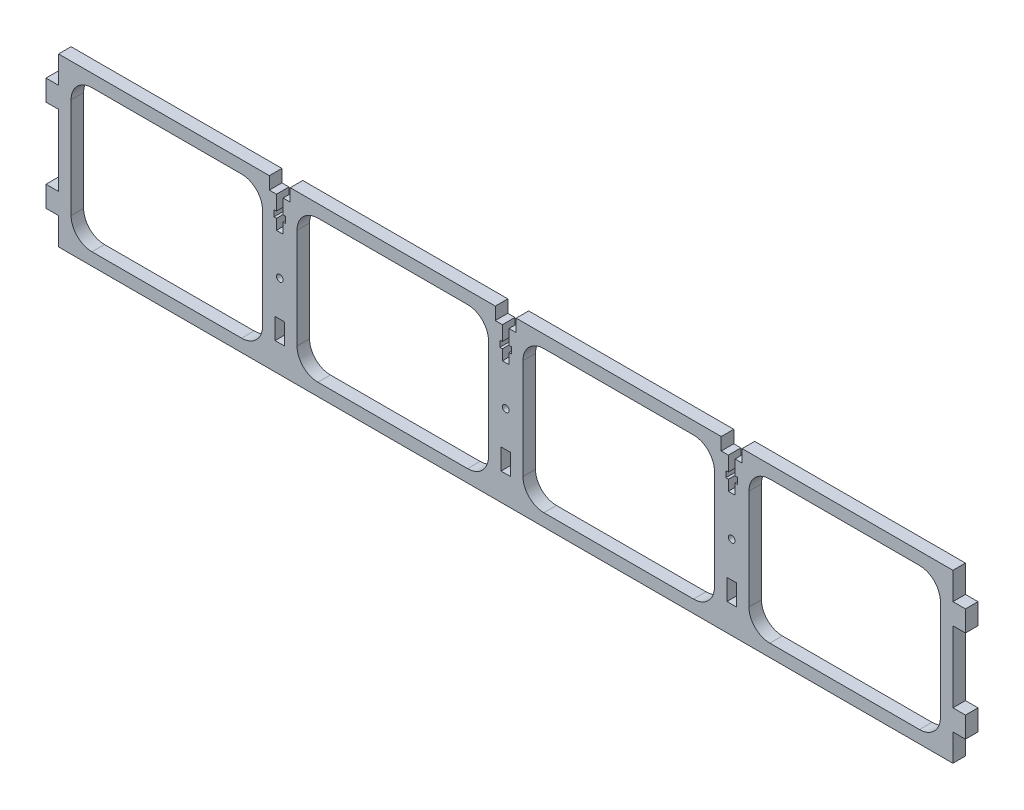
SolidWorks part; units mm, degrees
ref_plane "Front Plane" through (0, 0, 0) normal (0, 0, 1) x (1, 0, 0)
ref_plane "Top Plane" through (0, 0, 0) normal (0, 1, 0) x (1, 0, 0)
ref_plane "Right Plane" through (0, 0, 0) normal (1, 0, 0) x (0, 0, -1)
sketch "Sketch1" plane through (0, 0, 0) normal (0, 0, 1) x (1, 0, 0)
  line L1 (-214, -40) -> (214, -40)
  line L2 (-214, -40) -> (-214, 40)
  line L3 (-214, 40) -> (214, 40)
  line L4 (214, -40) -> (214, 40)
  line L5 (-214, -40) -> (214, 40) construction
  line L6 (-214, 40) -> (214, -40) construction
  point P0 (0, 0)
  dimension "D1" = 428
  dimension "D2" = 80
extrude "Boss-Extrude1" add sketch "Sketch1" along normal blind 6
sketch "Sketch2" plane through (0, 0, 6) normal (0, 0, 1) x (1, 0, 0)
  line L0 (-116.375, -40) -> (-116.375, -27) construction
  line L1 (-208, 40) -> (-208, -40) construction
  line L2 (-214, -34) -> (214, -34) construction
  line L3 (-214, -40) -> (214, -40) construction
  line L8 (214, -40) -> (214, 40)
  line L9 (214, 40) -> (-214, 40)
  line L10 (-214, 40) -> (-214, -40)
  line L11 (-214, -40) -> (214, -40)
  line L12 (214, -40) -> (214, 40) construction
  line L13 (214, 40) -> (-214, 40)
  line L14 (-214, 40) -> (-214, -40) construction
  line L15 (-208, -40) -> (214, -40) construction
  line L16 (-110.375, -40) -> (-110.375, -27) construction
  line L17 (-110.375, -40) -> (-110.375, -27) construction
  line L18 (-116.375, -24) -> (-116.375, 24)
  line L19 (-198, -34) -> (-126.375, -34)
  line L20 (-208, 24) -> (-208, -24)
  line L21 (-126.375, 34) -> (-198, 34)
  arc A0 (-198, 34) -> (-208, 24) centre (-198, 24) ccw
  arc A1 (-126.375, 34) -> (-116.375, 24) centre (-126.375, 24) cw
  arc A2 (-116.375, -24) -> (-126.375, -34) centre (-126.375, -24) cw
  arc A3 (-198, -34) -> (-208, -24) centre (-198, -24) cw
  dimension "D6" = 10
  dimension "D5" = 6
  dimension "D1" = 0
  dimension "D2" = 6
  dimension "D3" = 6
  dimension "D4" = 6
extrude "Cut-Extrude1" cut sketch "Sketch2" against normal up to next (6 mm away) contours L18 L21 L20 L19
pattern_linear "LPattern1" count 4 spacing 108.125 along (1, 0, 0) of "Cut-Extrude1"
sketch "Sketch3" plane through (0, 0, 0) normal (0, 0, -1) x (-1, 0, 0)
  line L8 (-110.375, -27) -> (-110.375, -17) construction
  line L9 (-110.375, -17) -> (-105.875, -17) construction
  line L11 (-105.875, -27) -> (-110.375, -27) construction
  line L24 (-110.375, -27) -> (-110.375, -17)
  line L25 (-110.375, -17) -> (-105.875, -17)
  line L26 (-105.875, -17) -> (-105.875, -27)
  line L27 (-105.875, -27) -> (-110.375, -27)
  line L44 (-2.25, -27) -> (-2.25, -17) construction
  line L45 (-2.25, -17) -> (2.25, -17) construction
  line L46 (2.25, -17) -> (2.25, -27) construction
  line L47 (2.25, -27) -> (-2.25, -27) construction
  line L52 (-2.25, -27) -> (-2.25, -17)
  line L53 (-2.25, -17) -> (2.25, -17)
  line L54 (2.25, -17) -> (2.25, -27)
  line L55 (2.25, -27) -> (-2.25, -27)
  line L60 (105.875, -27) -> (105.875, -17) construction
  line L61 (105.875, -17) -> (110.375, -17) construction
  line L62 (110.375, -17) -> (110.375, -27) construction
  line L63 (110.375, -27) -> (105.875, -27) construction
  line L68 (105.875, -27) -> (105.875, -17)
  line L69 (105.875, -17) -> (110.375, -17)
  line L70 (110.375, -17) -> (110.375, -27)
  line L71 (110.375, -27) -> (105.875, -27)
  circle A3 centre (108.125, 0) radius 1.6 construction
  circle A4 centre (0, 0) radius 1.6 construction
  circle A5 centre (-108.125, 0) radius 1.6 construction
  circle A6 centre (108.125, 0) radius 1.6
  circle A7 centre (0, 0) radius 1.6
  circle A8 centre (-108.125, 0) radius 1.6
extrude "Cut-Extrude2" cut sketch "Sketch3" against normal through all
sketch "Sketch4" plane through (0, 0, 0) normal (0, 0, -1) x (-1, 0, 0)
  line L0 (-111.5, 17) -> (-214, 17) construction
  line L1 (-214, -40) -> (-214, 40) construction
  line L2 (-108.5, 0) -> (-214, 0) construction
  line L3 (-220, 21.3321) -> (-220, 40) construction
  line L4 (-214, 17) -> (-220, 17)
  line L5 (-214, 17) -> (-214, 27)
  line L6 (-214, 27) -> (-220, 27)
  line L7 (-220, 17) -> (-220, 27)
  line L9 (-220, -17) -> (-220, -27)
  line L10 (-214, -27) -> (-220, -27)
  line L11 (-214, -17) -> (-214, -27)
  line L12 (-214, -17) -> (-220, -17)
  line L13 (0, 0) -> (0, 40) construction
  line L14 (-214, 40) -> (214, 40) construction
  line L15 (214, -17) -> (220, -17)
  line L16 (214, -17) -> (214, -27)
  line L17 (214, -27) -> (220, -27)
  line L18 (220, -17) -> (220, -27)
  line L19 (220, 17) -> (220, 27)
  line L20 (214, 27) -> (220, 27)
  line L21 (214, 17) -> (214, 27)
  line L22 (214, 17) -> (220, 17)
  point P13 (-108.5, -1)
  dimension "D1" = 34
  dimension "D2" = 10
extrude "Boss-Extrude2" add sketch "Sketch4" against normal blind 6
sketch "Sketch5" plane through (0, 40, 0) normal (0, 1, 0) x (1, 0, 0)
  line L0 (214, -6) -> (-214, -6) construction
  line L1 (-113.125, 0) -> (-103.125, 0)
  line L2 (-113.125, 0) -> (-113.125, -6)
  line L3 (-113.125, -6) -> (-103.125, -6)
  line L4 (-103.125, 0) -> (-103.125, -6)
  line L5 (-113.125, 0) -> (-103.125, -6) construction
  line L6 (-113.125, -6) -> (-103.125, 0) construction
  line L7 (-103.125, -6) -> (-103.125, 0) construction
  line L8 (5, -6) -> (5, 0) construction
  line L9 (-5, 0) -> (5, 0)
  line L10 (-5, 0) -> (-5, -6)
  line L11 (-5, -6) -> (5, -6)
  line L12 (5, 0) -> (5, -6)
  line L13 (-5, 0) -> (5, -6) construction
  line L14 (-5, -6) -> (5, 0) construction
  line L15 (113.125, -6) -> (113.125, 0) construction
  line L16 (103.125, 0) -> (113.125, 0)
  line L17 (103.125, 0) -> (103.125, -6)
  line L18 (103.125, -6) -> (113.125, -6)
  line L19 (113.125, 0) -> (113.125, -6)
  line L20 (103.125, 0) -> (113.125, -6) construction
  line L21 (103.125, -6) -> (113.125, 0) construction
  point P0 (-108.125, -3)
  point P10 (0, -3)
  point P18 (108.125, -3)
extrude "Cut-Extrude3" cut sketch "Sketch5" against normal blind 6
sketch "Sketch6" plane through (0, 0, 0) normal (0, 0, -1) x (-1, 0, 0)
  line L12 (-109.725, 34) -> (-109.725, 27)
  line L13 (-106.525, 34) -> (-109.725, 34)
  line L14 (-106.525, 27) -> (-106.525, 34)
  line L15 (-105.325, 27) -> (-106.525, 27)
  line L16 (-105.325, 24) -> (-105.325, 27)
  line L17 (-106.525, 24) -> (-105.325, 24)
  line L18 (-106.525, 19) -> (-106.525, 24)
  line L19 (-109.725, 19) -> (-106.525, 19)
  line L20 (-109.725, 24) -> (-109.725, 19)
  line L21 (-110.925, 24) -> (-109.725, 24)
  line L22 (-110.925, 27) -> (-110.925, 24)
  line L23 (-109.725, 27) -> (-110.925, 27)
  line L24 (-109.725, 34) -> (-109.725, 27)
  line L25 (-106.525, 34) -> (-109.725, 34)
  line L26 (-106.525, 27) -> (-106.525, 34)
  line L27 (-105.325, 27) -> (-106.525, 27)
  line L28 (-105.325, 24) -> (-105.325, 27)
  line L29 (-106.525, 24) -> (-105.325, 24)
  line L30 (-106.525, 19) -> (-106.525, 24)
  line L31 (-109.725, 19) -> (-106.525, 19)
  line L32 (-109.725, 24) -> (-109.725, 19)
  line L33 (-110.925, 24) -> (-109.725, 24)
  line L34 (-110.925, 27) -> (-110.925, 24)
  line L35 (-109.725, 27) -> (-110.925, 27)
  line L36 (-1.595, 27) -> (-2.795, 27)
  line L37 (-2.795, 27) -> (-2.795, 24)
  line L38 (-2.795, 24) -> (-1.595, 24)
  line L39 (-1.595, 24) -> (-1.595, 19)
  line L40 (-1.595, 19) -> (1.605, 19)
  line L41 (1.605, 19) -> (1.605, 24)
  line L42 (1.605, 24) -> (2.805, 24)
  line L43 (2.805, 24) -> (2.805, 27)
  line L44 (2.805, 27) -> (1.605, 27)
  line L45 (1.605, 27) -> (1.605, 34)
  line L46 (1.605, 34) -> (-1.595, 34)
  line L47 (-1.595, 34) -> (-1.595, 27)
  line L48 (-1.595, 27) -> (-2.795, 27)
  line L49 (-2.795, 27) -> (-2.795, 24)
  line L50 (-2.795, 24) -> (-1.595, 24)
  line L51 (-1.595, 24) -> (-1.595, 19)
  line L52 (-1.595, 19) -> (1.605, 19)
  line L53 (1.605, 19) -> (1.605, 24)
  line L54 (1.605, 24) -> (2.805, 24)
  line L55 (2.805, 24) -> (2.805, 27)
  line L56 (2.805, 27) -> (1.605, 27)
  line L57 (1.605, 27) -> (1.605, 34)
  line L58 (1.605, 34) -> (-1.595, 34)
  line L59 (-1.595, 34) -> (-1.595, 27)
  line L60 (106.535, 34) -> (106.535, 27)
  line L61 (109.735, 34) -> (106.535, 34)
  line L62 (109.735, 27) -> (109.735, 34)
  line L63 (110.935, 27) -> (109.735, 27)
  line L64 (110.935, 24) -> (110.935, 27)
  line L65 (109.735, 24) -> (110.935, 24)
  line L66 (109.735, 19) -> (109.735, 24)
  line L67 (106.535, 19) -> (109.735, 19)
  line L68 (106.535, 24) -> (106.535, 19)
  line L69 (105.335, 24) -> (106.535, 24)
  line L70 (105.335, 27) -> (105.335, 24)
  line L71 (106.535, 27) -> (105.335, 27)
  line L72 (106.535, 34) -> (106.535, 27)
  line L73 (109.735, 34) -> (106.535, 34)
  line L74 (109.735, 27) -> (109.735, 34)
  line L75 (110.935, 27) -> (109.735, 27)
  line L76 (110.935, 24) -> (110.935, 27)
  line L77 (109.735, 24) -> (110.935, 24)
  line L78 (109.735, 19) -> (109.735, 24)
  line L79 (106.535, 19) -> (109.735, 19)
  line L80 (106.535, 24) -> (106.535, 19)
  line L81 (105.335, 24) -> (106.535, 24)
  line L82 (105.335, 27) -> (105.335, 24)
  line L83 (106.535, 27) -> (105.335, 27)
  dimension "D1" = 0
  dimension "D2" = 0
  dimension "D3" = 0
extrude "Cut-Extrude4" cut sketch "Sketch6" against normal up to next
